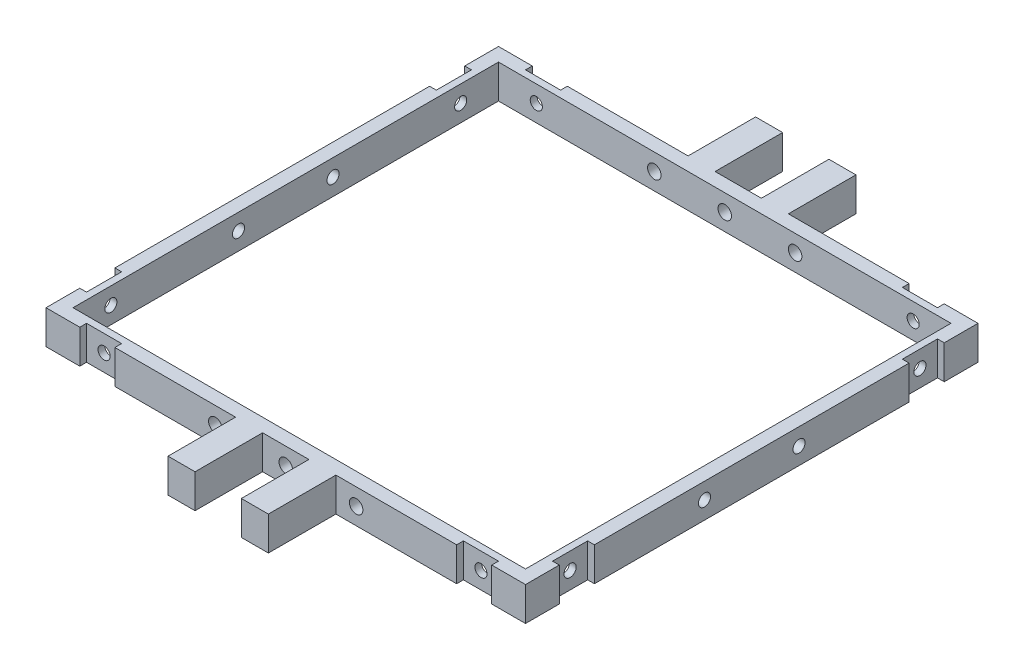
SolidWorks part; units mm, degrees
ref_plane "Front Plane" through (0, 0, 0) normal (0, 0, 1) x (1, 0, 0)
ref_plane "Top Plane" through (0, 0, 0) normal (0, 1, 0) x (1, 0, 0)
ref_plane "Right Plane" through (0, 0, 0) normal (1, 0, 0) x (0, 0, -1)
sketch "Sketch1" plane through (0, 0, 0) normal (0, 1, 0) x (1, 0, 0)
  line L1 (-35.5, 33.5) -> (35.5, 33.5)
  line L2 (-35.5, 33.5) -> (-35.5, -33.5)
  line L3 (-35.5, -33.5) -> (35.5, -33.5)
  line L4 (35.5, 33.5) -> (35.5, -33.5)
  line L5 (-35.5, 33.5) -> (35.5, -33.5) construction
  line L6 (-35.5, -33.5) -> (35.5, 33.5) construction
  line L7 (-33.5, 31.5) -> (33.5, 31.5)
  line L8 (-33.5, 31.5) -> (-33.5, -31.5)
  line L9 (-33.5, -31.5) -> (33.5, -31.5)
  line L10 (33.5, 31.5) -> (33.5, -31.5)
  line L11 (-33.5, 31.5) -> (33.5, -31.5) construction
  line L12 (-33.5, -31.5) -> (33.5, 31.5) construction
  point P0 (0, 0)
  point P6 (0, 0)
  dimension "D1" = 67
  dimension "D2" = 71
  dimension "D3" = 2
  dimension "D4" = 2
extrude "Boss-Extrude1" add sketch "Sketch1" along normal blind 5
sketch "Sketch2" plane through (35.5, 0, 0) normal (1, 0, 0) x (0, 0, -1)
  line L1 (-33.5, 5) -> (33.5, 5) construction
  circle A0 centre (-6.9997, 2.5914) radius 0.9
  circle A1 centre (7, 2.5) radius 0.9
  dimension "D1" = 14
  dimension "D2" = 2.5
  dimension "D3" = 7
  dimension "D4" = 1.8
  dimension "D5" = 1.8
  dimension "D6" = 6.9997
extrude "Cut-Extrude1" cut sketch "Sketch2" against normal blind 121
sketch "Sketch3" plane through (0, 0, 33.5) normal (0, 0, 1) x (1, 0, 0)
  line L0 (-35.5, 5) -> (35.5, 5) construction
  circle A0 centre (0, 2.5) radius 1
  dimension "D1" = 2
  dimension "D2" = 2.5
  dimension "D3" = 0
extrude "Cut-Extrude2" cut sketch "Sketch3" against normal blind 90
sketch "Sketch4" plane through (0, 0, 33.5) normal (0, 0, 1) x (1, 0, 0)
  line L0 (-35.5, 0) -> (35.5, 0) construction
  line L1 (3.425, 5) -> (7.425, 5)
  line L2 (3.425, 5) -> (3.425, 0)
  line L3 (3.425, 0) -> (7.425, 0)
  line L4 (7.425, 5) -> (7.425, 0)
  line L7 (-3.4289, 5) -> (-7.4289, 5)
  line L8 (-3.4289, 5) -> (-3.4289, 0)
  line L9 (-3.4289, 0) -> (-7.4289, 0)
  line L10 (-7.4289, 5) -> (-7.4289, 0)
  point P14 (22.845, 4.9091)
  point P17 (8.2361, 5.5355)
  point P18 (8.1655, 4.9091)
  dimension "D1" = 4
  dimension "D2" = 4
  dimension "D3" = 5
  dimension "D4" = 5
  dimension "D5" = 6.8539
  dimension "D6" = 0
  dimension "D7" = 0
  dimension "D8" = 3.425
extrude "Boss-Extrude2" add sketch "Sketch4" along normal blind 10
ref_plane "Plane1" through (0, 0, 0) normal (0, 0, 1) x (1, 0, 0)
mirror "Mirror1" about plane through (0, 0, 0) normal (0, 0, 1) of "Boss-Extrude2"
sketch "Sketch5" plane through (0, 0, 33.5) normal (0, 0, 1) x (1, 0, 0)
  line L0 (-7.4289, 5) -> (-7.4289, 0) construction
  line L1 (7.425, 0) -> (7.425, 5) construction
  line L2 (7.425, 5) -> (35.5, 5) construction
  line L3 (-35.5, 5) -> (-7.4289, 5) construction
  circle A0 centre (-10.4289, 2.5) radius 1
  circle A1 centre (10.425, 2.5) radius 1
  point P4 (0, 0)
  dimension "D1" = 3
  dimension "D2" = 3
  dimension "D3" = 2.5
  dimension "D4" = 2.5
  dimension "D5" = 2
  dimension "D6" = 2
extrude "Cut-Extrude3" cut sketch "Sketch5" against normal blind 109
sketch "Sketch9" plane through (0, 0, 33.5) normal (0, 0, 1) x (1, 0, 0)
  line L0 (-35.5, 5) -> (-7.4289, 5) construction
  line L1 (-30.5, 5) -> (-25.3, 5)
  line L2 (-30.5, 5) -> (-30.5, 0)
  line L3 (-30.5, 0) -> (-25.3, 0)
  line L4 (-25.3, 5) -> (-25.3, 0)
  line L5 (-35.5, 0) -> (-7.4289, 0) construction
  line L6 (7.425, 0) -> (35.5, 0) construction
  line L7 (30.5, 5) -> (25.3, 5)
  line L8 (30.5, 5) -> (30.5, 0)
  line L9 (30.5, 0) -> (25.3, 0)
  line L10 (25.3, 5) -> (25.3, 0)
  line L11 (-35.5, 5) -> (-35.5, 0) construction
  line L12 (35.5, 5) -> (35.5, 0) construction
  dimension "D1" = 5.2
  dimension "D2" = 5
  dimension "D3" = 5
  dimension "D4" = 5.2
extrude "Cut-Extrude6" cut sketch "Sketch9" against normal blind 1
sketch "Sketch10" plane through (35.5, 0, 0) normal (1, 0, 0) x (0, 0, -1)
  line L0 (-33.5, 5) -> (33.5, 5) construction
  line L1 (-28.5, 5) -> (-23.3, 5)
  line L2 (-28.5, 5) -> (-28.5, 0)
  line L3 (-28.5, 0) -> (-23.3, 0)
  line L4 (-23.3, 5) -> (-23.3, 0)
  line L5 (-33.5, 0) -> (33.5, 0) construction
  line L6 (33.5, 5) -> (33.5, 0) construction
  line L7 (28.5, 5) -> (23.3, 5)
  line L8 (28.5, 5) -> (28.5, 0)
  line L9 (28.5, 0) -> (23.3, 0)
  line L10 (23.3, 5) -> (23.3, 0)
  line L11 (-33.5, 5) -> (-33.5, 0) construction
  dimension "D1" = 5.2
  dimension "D2" = 5.2
  dimension "D3" = 5
  dimension "D4" = 5
extrude "Cut-Extrude7" cut sketch "Sketch10" against normal blind 1
ref_plane "Plane2" through (0, 0, 0) normal (1, 0, 0) x (0, 0, -1)
mirror "Mirror2" about plane through (0, 0, 0) normal (1, 0, 0) of "Cut-Extrude7"
mirror "Mirror3" about plane through (0, 0, 0) normal (0, 0, 1) of "Cut-Extrude6"
sketch "Sketch11" plane through (34.5, 0, 0) normal (1, 0, 0) x (0, 0, -1)
  circle A0 centre (25.9, 2.5) radius 0.9
  circle A1 centre (-25.9, 2.5) radius 0.9
  dimension "D1" = 1.8
  dimension "D2" = 1.8
extrude "Cut-Extrude8" cut sketch "Sketch11" against normal blind 81
sketch "Sketch12" plane through (0, 0, 32.5) normal (0, 0, 1) x (1, 0, 0)
  circle A0 centre (27.9, 2.5) radius 0.9
  circle A1 centre (-27.9, 2.5) radius 0.9
  dimension "D1" = 1.8
  dimension "D2" = 1.8
extrude "Cut-Extrude9" cut sketch "Sketch12" against normal blind 81
